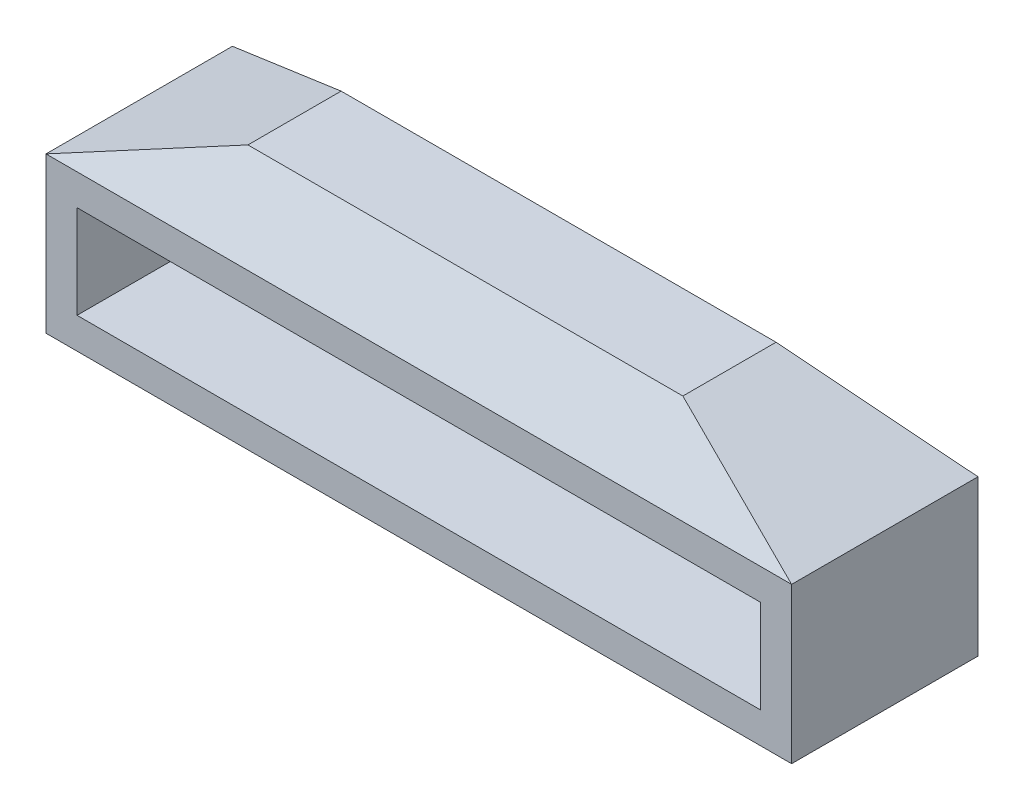
SolidWorks part; units mm, degrees
ref_plane "Front Plane" through (0, 0, 0) normal (0, 0, 1) x (1, 0, 0)
ref_plane "Top Plane" through (0, 0, 0) normal (0, 1, 0) x (1, 0, 0)
ref_plane "Right Plane" through (0, 0, 0) normal (1, 0, 0) x (0, 0, -1)
sketch "Sketch1" plane through (0, 0, 0) normal (0, 0, 1) x (1, 0, 0)
  line L0 (-12, 0) -> (12, 0)
  line L1 (12, 0) -> (12, 5)
  line L2 (12, 5) -> (-12, 5)
  line L3 (-12, 5) -> (-12, 0)
  line L4 (-11, 1) -> (11, 1)
  line L5 (11, 1) -> (11, 4)
  line L6 (11, 4) -> (-11, 4)
  line L7 (-11, 4) -> (-11, 1)
  point P7 (0, 0)
  point P10 (0, 0)
  dimension "D1" = 1
  dimension "D2" = 3
  dimension "D3" = 1
  dimension "D4" = 1
  dimension "D5" = 1
  dimension "D6" = 22
extrude "Boss-Extrude1" add sketch "Sketch1" along normal blind 6
ref_plane "Plane1" through (0, 7, 0) normal (0, 1, 0) x (1, 0, 0)
sketch "Sketch2" plane through (0, 7, 0) normal (0, 1, 0) x (1, 0, 0)
  line L0 (-7, -1.5) -> (-7, -4.5)
  line L1 (-7, -4.5) -> (7, -4.5)
  line L2 (7, -4.5) -> (7, -1.5)
  line L3 (7, -1.5) -> (-7, -1.5)
  line L12 (12, 0) -> (-12, 0) construction
  line L13 (12, 0) -> (-12, 0) construction
  line L14 (-12, -6) -> (-12, 0) construction
  line L15 (-12, -6) -> (-12, 0) construction
  point P6 (0, -1.5)
  point P7 (0, 0)
  point P10 (-7, -3)
  point P11 (-12, -3)
  dimension "D1" = 14
  dimension "D2" = 3
loft "Loft1" add profiles "Sketch2" section face at (0, 5, 3) section "Sketch2"
sketch "Sketch5" plane through (0, 0, 0) normal (1, 0, 0) x (0, 0, -1)
  line L0 (-6, 4) -> (0, 4) construction
  line L1 (-6, 4) -> (0, 4) construction
  line L3 (-4.5, 7) -> (-1.5, 7) construction
  circle A0 centre (-3, 5.2247) radius 1.25
  point P2 (-2.75, 4)
  point P5 (-3.25, 4)
  point P6 (-3, 4)
  point P7 (0, 0)
  dimension "D1" = 2.5
  dimension "D3" = 0.5253
  dimension "D2" = 0.5
extrude "Cut-Extrude1" cut sketch "Sketch5" against normal mid plane 12
